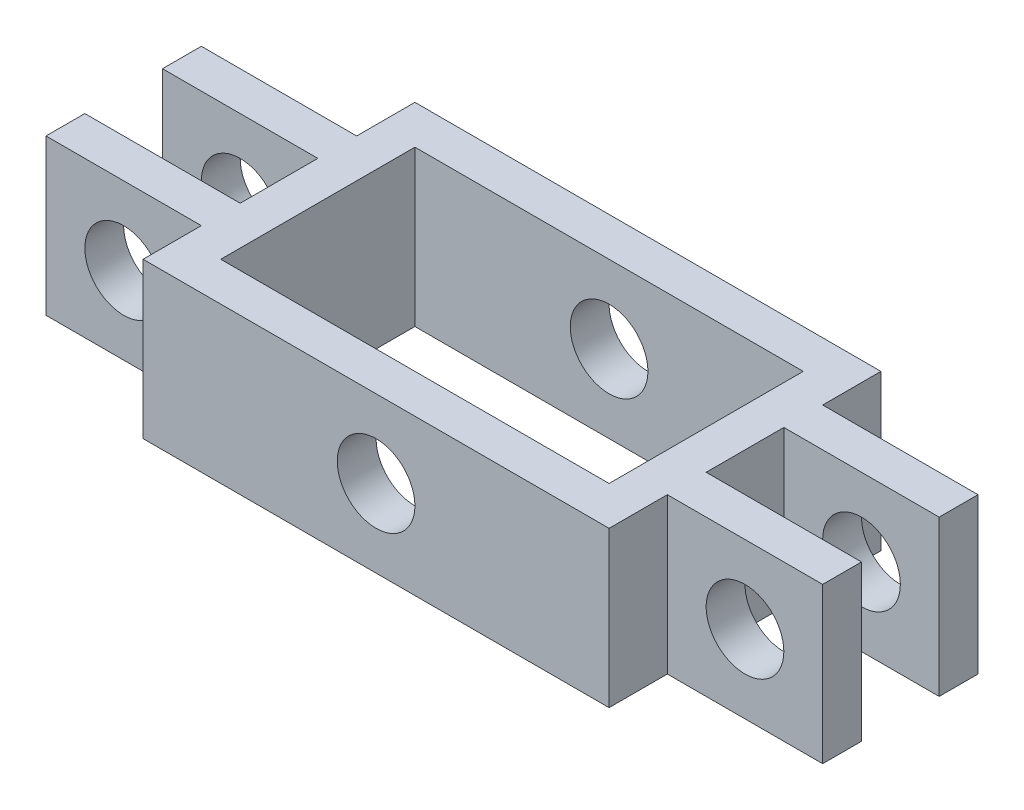
SolidWorks part; units mm, degrees
ref_plane "Front Plane" through (0, 0, 0) normal (0, 0, 1) x (1, 0, 0)
ref_plane "Top Plane" through (0, 0, 0) normal (0, 1, 0) x (1, 0, 0)
ref_plane "Right Plane" through (0, 0, 0) normal (1, 0, 0) x (0, 0, -1)
sketch "Sketch2" plane through (0, 0, 0) normal (0, 1, 0) x (1, 0, 0)
  line L1 (-25, -12.5) -> (25, -12.5)
  line L2 (-25, -12.5) -> (-25, 12.5)
  line L3 (-25, 12.5) -> (25, 12.5)
  line L4 (25, -12.5) -> (25, 12.5)
  line L5 (-25, -12.5) -> (25, 12.5) construction
  line L6 (-25, 12.5) -> (25, -12.5) construction
  line L7 (-30, -17.5) -> (30, -17.5)
  line L8 (-30, -17.5) -> (-30, 17.5)
  line L9 (-30, 17.5) -> (30, 17.5)
  line L10 (30, -17.5) -> (30, 17.5)
  line L11 (-30, -17.5) -> (30, 17.5) construction
  line L12 (-30, 17.5) -> (30, -17.5) construction
  point P0 (0, 0)
  point P6 (0, 0)
  dimension "D1" = 25
  dimension "D2" = 50
  dimension "D3" = 35
  dimension "D4" = 60
extrude "Boss-Extrude1" add sketch "Sketch2" along normal blind 20
sketch "Sketch3" plane through (0, 0, 17.5) normal (0, 0, 1) x (1, 0, 0)
  line L0 (-30, 20) -> (-30, 0) construction
  line L1 (-30, 0) -> (30, 0) construction
  circle A0 centre (0, 10) radius 5
  dimension "D3" = 10
  dimension "D1" = 30
  dimension "D2" = 10
extrude "Cut-Extrude1" cut sketch "Sketch3" against normal through all
sketch "Sketch4" plane through (-30, 0, 0) normal (-1, 0, 0) x (0, 0, 1)
  line L0 (-17.5, 20) -> (-17.5, 0) construction
  line L1 (10, 0) -> (-10, 0)
  line L2 (10, 0) -> (10, 20)
  line L3 (10, 20) -> (-10, 20)
  line L4 (-10, 0) -> (-10, 20)
  line L5 (10, 0) -> (-10, 20) construction
  line L6 (10, 20) -> (-10, 0) construction
  line L7 (-17.5, 0) -> (17.5, 0) construction
  point P0 (0, 10)
  dimension "D1" = 20
  dimension "D2" = 20
  dimension "D3" = 7.5
  dimension "D4" = 0
extrude "Boss-Extrude2" add sketch "Sketch4" along normal blind 20
sketch "Sketch5" plane through (30, 0, 0) normal (1, 0, 0) x (0, 0, -1)
  line L0 (-17.5, 20) -> (17.5, 20) construction
  line L1 (-10, 20) -> (10, 20)
  line L2 (-10, 20) -> (-10, 0)
  line L3 (-10, 0) -> (10, 0)
  line L4 (10, 20) -> (10, 0)
  line L5 (-17.5, 0) -> (17.5, 0) construction
  line L6 (-17.5, 20) -> (-17.5, 0) construction
  dimension "D1" = 7.5
  dimension "D2" = 20
extrude "Boss-Extrude3" add sketch "Sketch5" along normal blind 20
sketch "Sketch6" plane through (0, 0, 10) normal (0, 0, 1) x (1, 0, 0)
  line L0 (-50, 20) -> (-30, 20) construction
  line L1 (-50, 0) -> (-50, 20) construction
  line L2 (50, 20) -> (50, 0) construction
  line L3 (50, 0) -> (30, 0) construction
  circle A0 centre (-40, 10) radius 5
  circle A1 centre (40, 10) radius 5
  dimension "D3" = 10
  dimension "D4" = 10
  dimension "D5" = 10
  dimension "D6" = 10
  dimension "D1" = 10
  dimension "D2" = 10
extrude "Cut-Extrude2" cut sketch "Sketch6" against normal through all
sketch "Sketch7" plane through (0, 20, 0) normal (0, 1, 0) x (1, 0, 0)
  line L0 (50, 10) -> (50, -10) construction
  line L1 (50, 5) -> (30, 5)
  line L2 (50, 5) -> (50, -5)
  line L3 (50, -5) -> (30, -5)
  line L4 (30, 5) -> (30, -5)
  line L5 (-50, -10) -> (-50, 10) construction
  line L6 (-50, 5) -> (-30, 5)
  line L7 (-50, 5) -> (-50, -5)
  line L8 (-50, -5) -> (-30, -5)
  line L9 (-30, 5) -> (-30, -5)
  line L10 (50, 10) -> (30, 10) construction
  line L11 (-50, 10) -> (-30, 10) construction
  dimension "D1" = 10
  dimension "D2" = 5
  dimension "D3" = 5
  dimension "D4" = 10
  dimension "D5" = 20
  dimension "D6" = 20
extrude "Cut-Extrude3" cut sketch "Sketch7" against normal through all
